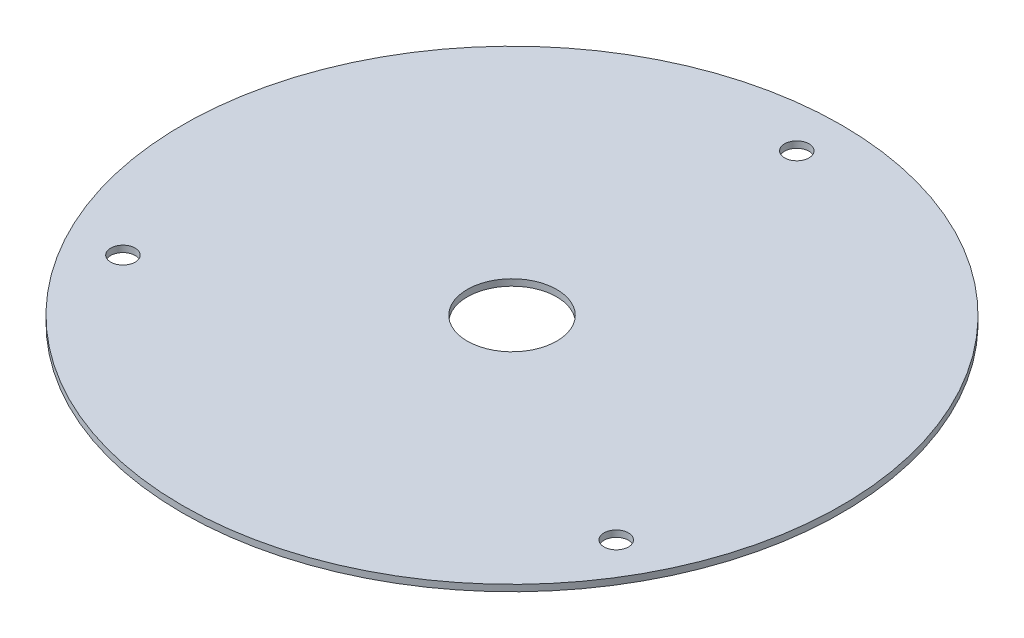
SolidWorks part; units mm, degrees
material "6061 Alloy"
ref_plane "Front Plane" through (0, 0, 0) normal (0, 0, 1) x (1, 0, 0)
ref_plane "Top Plane" through (0, 0, 0) normal (0, 1, 0) x (1, 0, 0)
ref_plane "Right Plane" through (0, 0, 0) normal (1, 0, 0) x (0, 0, -1)
sketch "Sketch1" plane through (0, 0, 0) normal (0, 1, 0) x (1, 0, 0)
  line L0 (0, 0) -> (0, 70) construction
  circle A0 centre (0, 0) radius 81
  circle A1 centre (0, 0) radius 11
  circle A2 centre (0, 70) radius 3
  circle A3 centre (60.6218, -35) radius 3
  circle A4 centre (-60.6218, -35) radius 3
  dimension "D1" = 162
  dimension "D2" = 22
  dimension "D3" = 6
  dimension "D4" = 70
  dimension "D6" = 70
  dimension "D5" = 3
extrude "Boss-Extrude1" add sketch "Sketch1" along normal blind 1.5875
